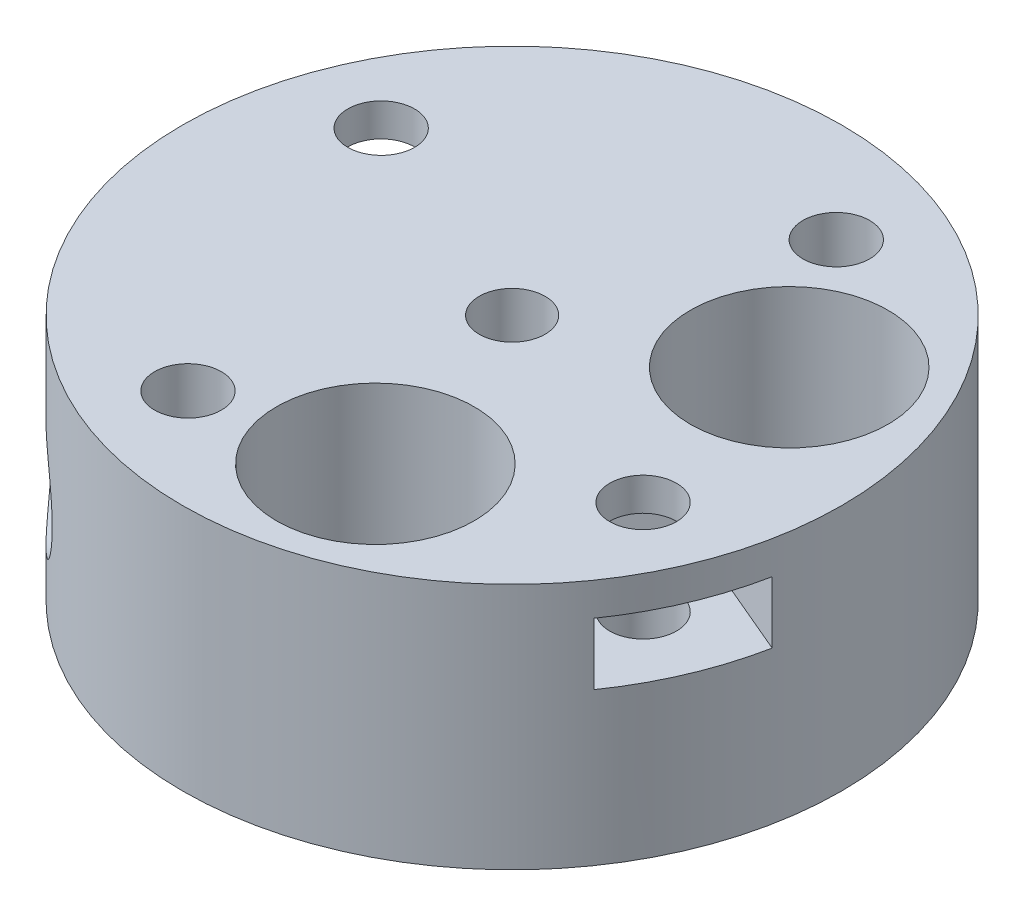
SolidWorks part; units mm, degrees
ref_plane "Front Plane" through (0, 0, 0) normal (0, 0, 1) x (1, 0, 0)
ref_plane "Top Plane" through (0, 0, 0) normal (0, 1, 0) x (1, 0, 0)
ref_plane "Right Plane" through (0, 0, 0) normal (1, 0, 0) x (0, 0, -1)
sketch "Sketch1" plane through (0, 0, 0) normal (0, 1, 0) x (1, 0, 0)
  circle A0 centre (0, 0) radius 20
  dimension "D1" = 40
extrude "Boss-Extrude1" add sketch "Sketch1" along normal mid plane 15
sketch "Sketch4" plane through (0, -7.5, 0) normal (0, -1, 0) x (1, 0, 0)
  circle A0 centre (0, 0) radius 5.125
  dimension "D1" = 10.25
extrude "Cut-Extrude2" cut sketch "Sketch4" against normal offset from surface (12.15 mm away) 2.85 up to face at (0, 7.5, 20)
sketch "Sketch5" plane through (0, 7.5, 0) normal (0, 1, 0) x (1, 0, 0)
  circle A0 centre (0, 0) radius 2
  dimension "D1" = 4
extrude "Cut-Extrude3" cut sketch "Sketch5" against normal through all both and the other way through all
sketch "Sketch2" plane through (0, 7.5, 0) normal (0, 1, 0) x (1, 0, 0)
  line L0 (0, 0) -> (0, 20) construction
  line L1 (0, 0) -> (-13.8076, 5.861) construction
  circle A0 centre (0, 0) radius 20 construction
  circle A1 centre (-13.8076, 5.861) radius 2.025
  dimension "D1" = 4.05
  dimension "D2" = 15
  dimension "D3" = 67
extrude "Cut-Extrude1" cut sketch "Sketch2" against normal through all
pattern_circular "CirPattern1" count 4 over 360 about axis through (0, 0, 0) along (0, 1, 0) of "Cut-Extrude1"
sketch "Sketch6" plane through (0, 0, 0) normal (0, 0, 1) x (1, 0, 0)
  line L0 (0, 7.5) -> (0, -7.5) construction
  line L1 (20, 7.5) -> (-20, 7.5) construction
  line L2 (-20, -7.5) -> (20, -7.5) construction
  line L3 (-20, 4.65) -> (20, 4.65) construction
  line L4 (-20, 7.5) -> (-20, -7.5) construction
  line L5 (20, -7.5) -> (20, 7.5) construction
  circle A0 centre (0, -1.35) radius 1.525
  dimension "D1" = 3.05
  dimension "D2" = 2.85
  dimension "D3" = 6
extrude "Cut-Extrude4" cut sketch "Sketch6" against normal through all
sketch "Sketch7" plane through (0, 0, 0) normal (0, 0, 1) x (1, 0, 0)
  circle A0 centre (0, -1.35) radius 3.25
  dimension "D1" = 6.5
extrude "Cut-Extrude5" cut sketch "Sketch7" along normal blind 8 from offset 20 offset against normal yes
sketch "Sketch9" plane through (0, 0, 0) normal (0, 0, 1) x (1, 0, 0)
  line L0 (20, -7.5) -> (20, 7.5) construction
  line L1 (0, -4.9584) -> (3.125, -3.1542) construction
  line L2 (3.125, -3.1542) -> (3.125, 0.4542)
  line L3 (3.125, 0.4542) -> (0, 2.2584)
  line L4 (0, 2.2584) -> (-3.125, 0.4542)
  line L5 (-3.125, 0.4542) -> (-3.125, -3.1542)
  line L6 (-3.125, -3.1542) -> (0, -4.9584) construction
  line L7 (3.125, -3.1542) -> (-3.125, -3.1542) construction
  line L8 (3.125, -3.1542) -> (3.125, -7.6706)
  line L9 (-3.125, -3.1542) -> (-3.125, -7.6706)
  line L10 (3.125, -7.6706) -> (-3.125, -7.6706)
  circle A0 centre (0, -1.35) radius 3.125 construction
  point P11 (0, 0)
  point P12 (0, 0)
  dimension "D1" = 6.25
extrude "Cut-Extrude11" cut sketch "Sketch9" against normal blind 2.85 from offset 6.5 offset against normal yes
pattern_circular "CirPattern2" count 2 every 135 about axis through (0, 0, 0) along (0, 1, 0) of "Cut-Extrude4", "Cut-Extrude5", "Cut-Extrude11"
sketch "Sketch8" plane through (0, 0, 0) normal (0, 1, 0) x (1, 0, 0)
  line L0 (0, 0) -> (-13.8076, 5.861) construction
  line L1 (-9.4231, 3.9999) -> (-10.0036, 8.7275)
  line L2 (-10.0036, 8.7275) -> (-14.3881, 10.5886)
  line L3 (-14.3881, 10.5886) -> (-18.1921, 7.7221) construction
  line L4 (-18.1921, 7.7221) -> (-17.6116, 2.9944) construction
  line L5 (-17.6116, 2.9944) -> (-13.2271, 1.1333)
  line L6 (-13.2271, 1.1333) -> (-9.4231, 3.9999)
  line L7 (-14.3881, 10.5886) -> (-17.6116, 2.9944) construction
  line L8 (-14.3881, 10.5886) -> (-19.5664, 12.7867)
  line L9 (-17.6116, 2.9944) -> (-22.7899, 5.1925)
  line L10 (-19.5664, 12.7867) -> (-22.7899, 5.1925)
  circle A0 centre (-13.8076, 5.861) radius 4.125 construction
  dimension "D1" = 8.25
extrude "Cut-Extrude7" cut sketch "Sketch8" against normal blind 3.75 from offset 5.5
pattern_circular "CirPattern3" count 2 over 360 about axis through (0, 0, 0) along (0, 1, 0) of "Cut-Extrude7"
sketch "Sketch10" plane through (0, 7.5, 0) normal (0, 1, 0) x (1, 0, 0)
  line L0 (0, 0) -> (0, -20) construction
  line L1 (0, 0) -> (3.6546, -11.9538) construction
  circle A0 centre (0, 0) radius 20 construction
  circle A1 centre (3.6546, -11.9538) radius 6
  dimension "D1" = 12
  dimension "D2" = 17
  dimension "D3" = 12.5
extrude "Cut-Extrude12" cut sketch "Sketch10" against normal through all both and the other way through all
pattern_circular "CirPattern4" count 2 every 100 about axis through (0, 7.5, 0) along (0, 1, 0) of "Cut-Extrude12"
